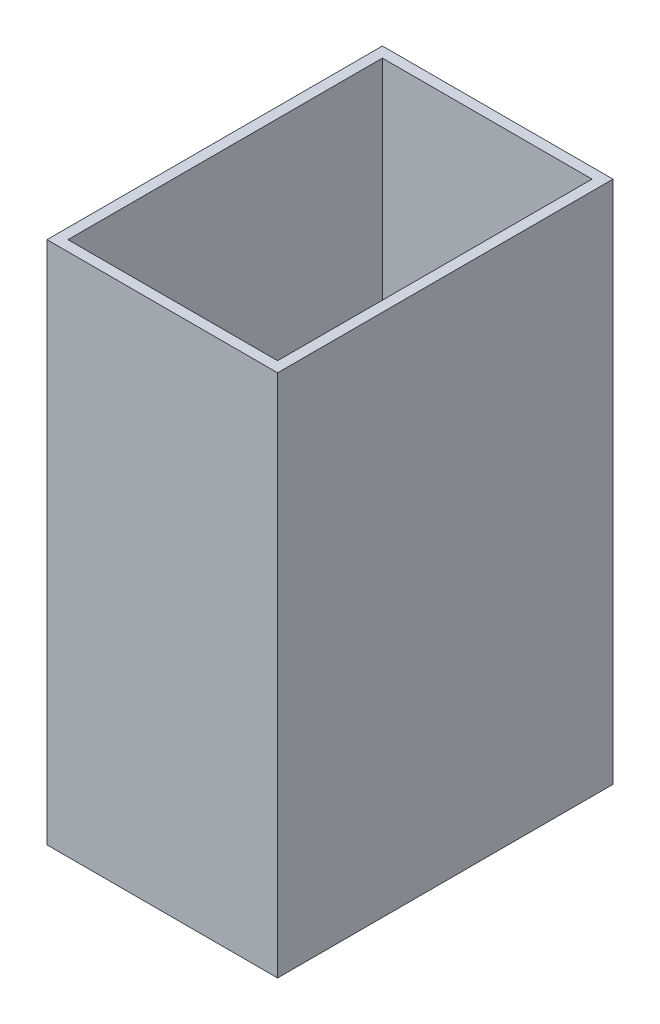
SolidWorks part; units mm, degrees
ref_plane "前视基准面" through (0, 0, 0) normal (0, 0, 1) x (1, 0, 0)
ref_plane "上视基准面" through (0, 0, 0) normal (0, 1, 0) x (1, 0, 0)
ref_plane "右视基准面" through (0, 0, 0) normal (1, 0, 0) x (0, 0, -1)
sketch "草图2" plane through (0, 0, 0) normal (0, 1, 0) x (1, 0, 0)
  line L1 (-100, 150) -> (100, 150)
  line L2 (-100, 150) -> (-100, -150)
  line L3 (-100, -150) -> (100, -150)
  line L4 (100, 150) -> (100, -150)
  line L5 (-100, 150) -> (100, -150) construction
  line L6 (-100, -150) -> (100, 150) construction
  line L7 (-110, 160) -> (110, 160)
  line L8 (-110, 160) -> (-110, -160)
  line L9 (-110, -160) -> (110, -160)
  line L10 (110, 160) -> (110, -160)
  line L11 (-110, 160) -> (110, -160) construction
  line L12 (-110, -160) -> (110, 160) construction
  point P0 (0, 0)
  point P6 (0, 0)
  dimension "D1" = 200
  dimension "D2" = 300
  dimension "D3" = 10
  dimension "D4" = 10
extrude "凸台-拉伸2" add sketch "草图2" along normal blind 500
